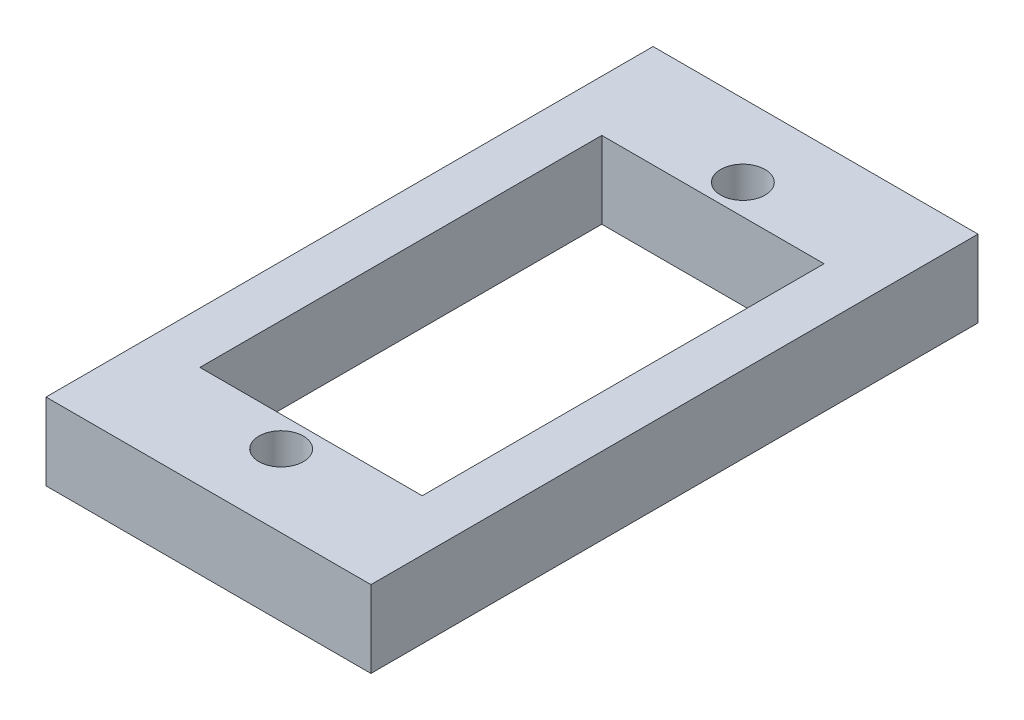
SolidWorks part; units mm, degrees
ref_plane "Front Plane" through (0, 0, 0) normal (0, 0, 1) x (1, 0, 0)
ref_plane "Top Plane" through (0, 0, 0) normal (0, 1, 0) x (1, 0, 0)
ref_plane "Right Plane" through (0, 0, 0) normal (1, 0, 0) x (0, 0, -1)
sketch "Sketch1" plane through (0, 0, 0) normal (0, 1, 0) x (1, 0, 0)
  line L1 (-6.5, -11.75) -> (6.5, -11.75)
  line L2 (-6.5, -11.75) -> (-6.5, 11.75)
  line L3 (-6.5, 11.75) -> (6.5, 11.75)
  line L4 (6.5, -11.75) -> (6.5, 11.75)
  line L5 (-6.5, -11.75) -> (6.5, 11.75) construction
  line L6 (-6.5, 11.75) -> (6.5, -11.75) construction
  line L7 (-9.5, -17.75) -> (9.5, -17.75)
  line L8 (-9.5, -17.75) -> (-9.5, 17.75)
  line L9 (-9.5, 17.75) -> (9.5, 17.75)
  line L10 (9.5, -17.75) -> (9.5, 17.75)
  line L11 (-9.5, -17.75) -> (9.5, 17.75) construction
  line L12 (-9.5, 17.75) -> (9.5, -17.75) construction
  circle A0 centre (0, 13.5) radius 1.3
  circle A1 centre (0, -13.5) radius 1.3
  point P0 (0, 0)
  point P6 (0, 0)
  point P15 (0, 0)
  point P16 (0, 0)
  point P17 (0, 0)
  dimension "D5" = 13.5
  dimension "D7" = 2.6
  dimension "D8" = 2.6
  dimension "D9" = 9.5
  dimension "D10" = 9.5
  dimension "D1" = 13
  dimension "D2" = 23.5
  dimension "D3" = 3
  dimension "D4" = 6
  dimension "D6" = 13.5
extrude "Boss-Extrude1" add sketch "Sketch1" along normal blind 4.5
